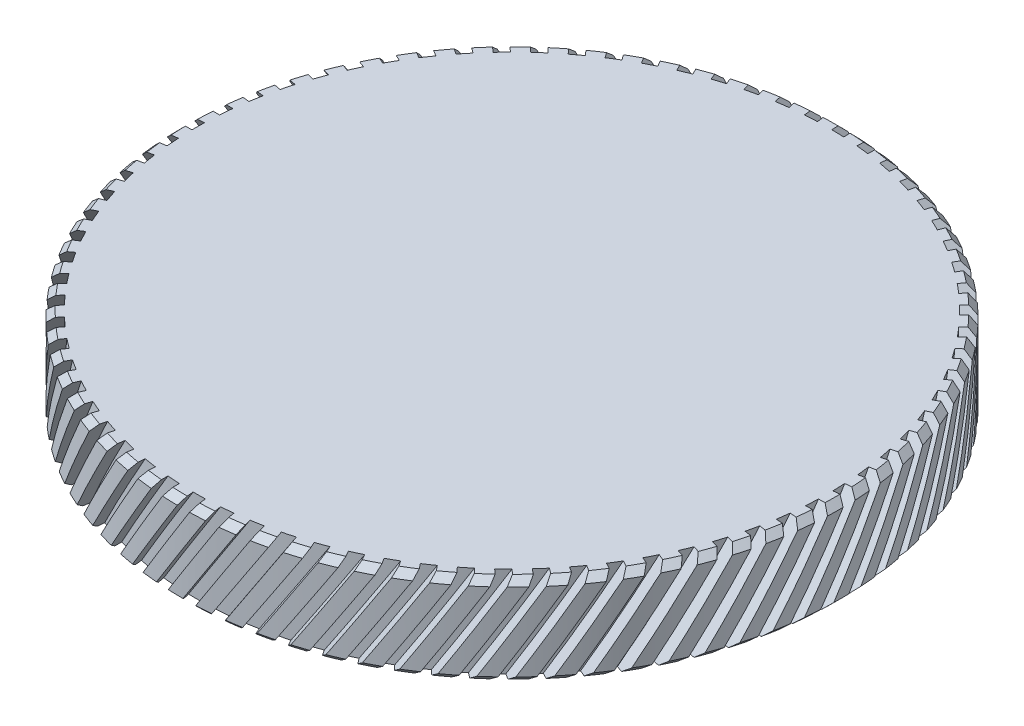
SolidWorks part; units mm, degrees
ref_plane "前视基准面" through (0, 0, 0) normal (0, 0, 1) x (1, 0, 0)
ref_plane "上视基准面" through (0, 0, 0) normal (0, 1, 0) x (1, 0, 0)
ref_plane "右视基准面" through (0, 0, 0) normal (1, 0, 0) x (0, 0, -1)
sketch "草图1" plane through (0, 0, 0) normal (0, 0, 1) x (1, 0, 0)
  line L0 (0, 46.0207) -> (0, -69.6142) construction
  line L1 (20.5, -8.8309) -> (21.1, -8.8309)
  line L2 (25.4, -6.3309) -> (0, -6.3309)
  line L3 (20.5, -13.3309) -> (25.4, -13.3309)
  line L4 (20.5, -13.3309) -> (20.5, -8.8309)
  line L5 (21.1, -8.8309) -> (21.1, -7.8309)
  line L6 (25.4, -13.3309) -> (25.4, -6.3309)
  line L7 (21.1, -7.8309) -> (0, -7.8309)
  line L8 (0, -7.8309) -> (0, -6.3309)
  dimension "D1" = 21.1
  dimension "D2" = 7
  dimension "D3" = 25.4
  dimension "D4" = 20.5
  dimension "D5" = 4.5
  dimension "D6" = 5.5
revolve "旋转1" add sketch "草图1" angle 360 about L0
cosmetic thread "装饰螺纹线1" parameters "D2"=42
chamfer "倒角1" distance 0.5 angle 45 2 edges at (0, -6.3309, 25.4) (0, -13.3309, 25.4)
surface "曲面-等距1" parameters "D1"=1
sketch "草图2" plane through (0, 0, 0) normal (0, 0, 1) x (1, 0, 0)
  line L0 (0, -2.7759) -> (-6.5923, -13.3309)
  line L1 (0, -2.7759) -> (0.6785, -3.1997)
  line L2 (-6.5923, -13.3309) -> (-5.9138, -13.7547)
  line L3 (0.6785, -3.1997) -> (-5.9138, -13.7547)
  line L4 (-24.9, -13.3309) -> (24.9, -13.3309) construction
extrude "切除-拉伸1" cut sketch "草图2" against normal up to surface (5.6 mm away) from offset 30
pattern_circular "阵列(圆周)1" count 75 over 360 about axis through (0, 0, 0) along (0, 1, 0) of "切除-拉伸1"
delete or keep bodies "实体-删除/保留 1" type delete bodies bodies 107
